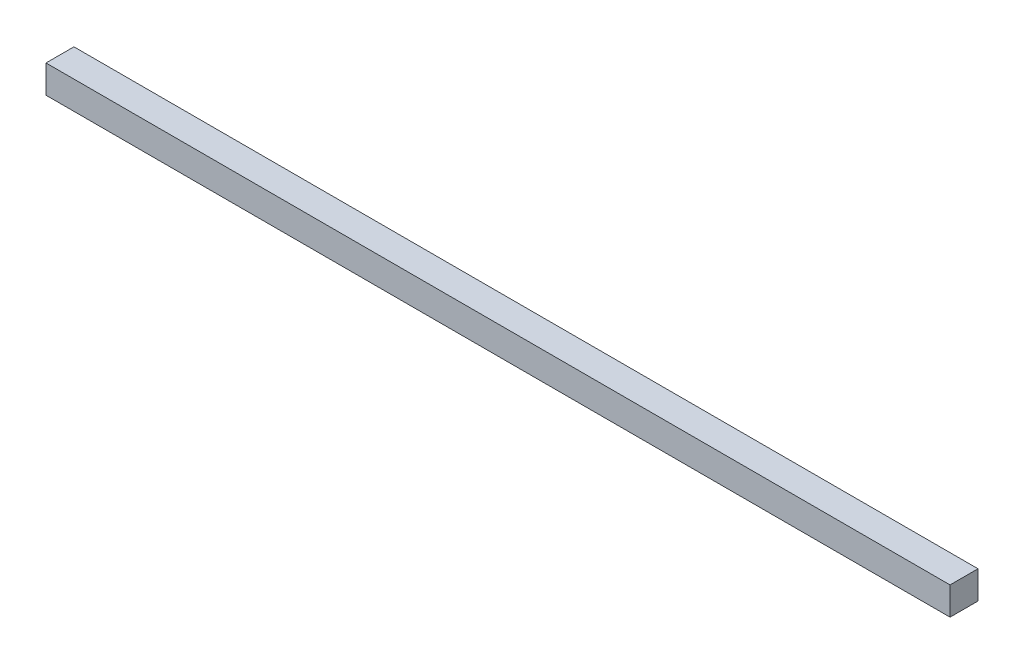
SolidWorks part; units mm, degrees
material "Plywood"
ref_plane "Front Plane" through (0, 0, 0) normal (0, 0, 1) x (1, 0, 0)
ref_plane "Top Plane" through (0, 0, 0) normal (0, 1, 0) x (1, 0, 0)
ref_plane "Right Plane" through (0, 0, 0) normal (1, 0, 0) x (0, 0, -1)
sketch "Sketch1" plane through (0, 0, 0) normal (1, 0, 0) x (0, 0, -1)
  line L1 (0, 0) -> (9.525, 0)
  line L2 (0, 0) -> (0, 9.525)
  line L3 (0, 9.525) -> (9.525, 9.525)
  line L4 (9.525, 0) -> (9.525, 9.525)
  dimension "D1" = 9.525
extrude "Boss-Extrude1" add sketch "Sketch1" against normal blind 307.975 contours L1 L4 L3 L2
move or copy body "Body-Move/Copy1" [suppressed] bodies to move or copy 101 parameters "D1"=0, "D2"=0, "D3"=0
move or copy body "Body-Move/Copy2" [suppressed] bodies to move or copy 102 parameters "D1"=0, "D2"=0, "D3"=0
move or copy body "Body-Move/Copy3" [suppressed] bodies to move or copy 103 parameters "D1"=0, "D2"=0, "D3"=0
move or copy body "Body-Move/Copy4" [suppressed] bodies to move or copy 104 parameters "D1"=0, "D2"=0, "D3"=0
